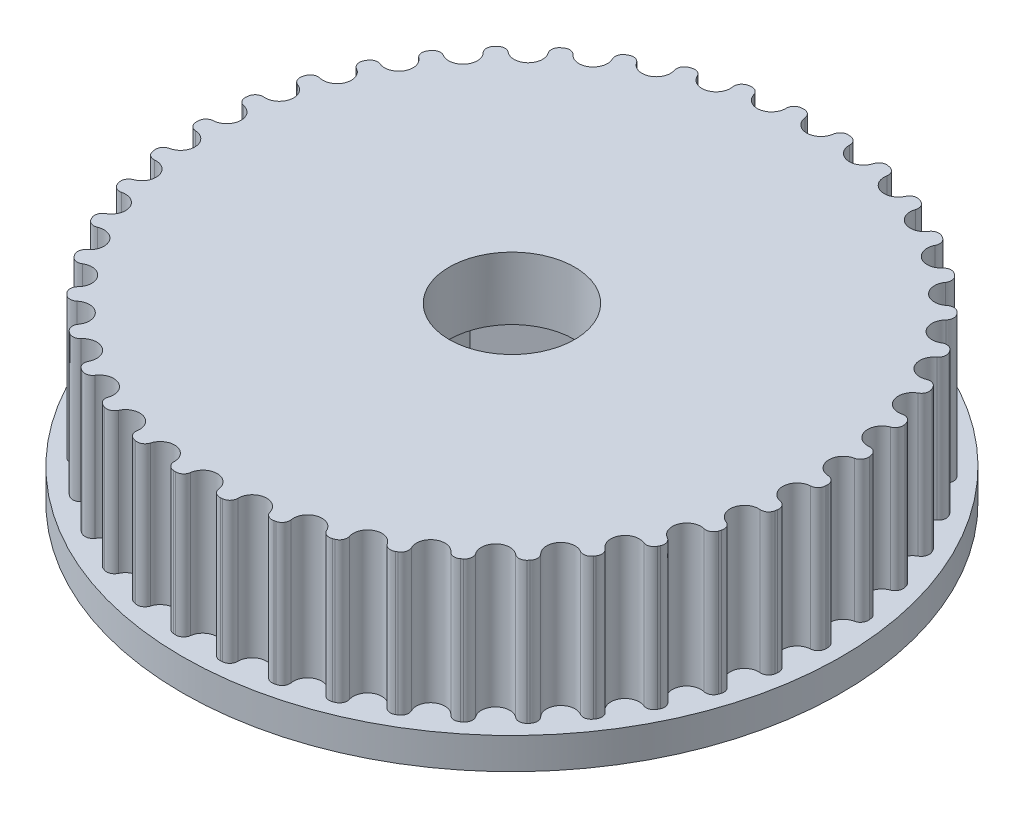
SolidWorks part; units mm, degrees
ref_plane "Front Plane" through (0, 0, 0) normal (0, 0, 1) x (1, 0, 0)
ref_plane "Top Plane" through (0, 0, 0) normal (0, 1, 0) x (1, 0, 0)
ref_plane "Right Plane" through (0, 0, 0) normal (1, 0, 0) x (0, 0, -1)
sketch "Эскиз1" plane through (0, 0, 0) normal (0, 1, 0) x (1, 0, 0)
  circle A0 centre (0, 0) radius 21
  dimension "D1" = 42
extrude "Бобышка-Вытянуть1" add sketch "Эскиз1" along normal blind 2
sketch "Эскиз2" plane through (0, 2, 0) normal (0, 1, 0) x (1, 0, 0)
  circle A0 centre (0, 0) radius 20.065
  dimension "D1" = 40.13
extrude "Бобышка-Вытянуть2" add sketch "Эскиз2" along normal blind 9
sketch "Эскиз3" plane through (0, 11, 0) normal (0, 1, 0) x (1, 0, 0)
  line L0 (0, 0) -> (-1.0785, 23.3144)
  line L1 (0, 0) -> (1.0782, 23.3144)
  line L2 (1.0782, 23.3144) -> (-1.0785, 23.3144)
  circle A0 centre (0, 0) radius 20.065
  circle A1 centre (0, 0) radius 18.785
  circle A2 centre (-0.0001, 19.695) radius 0.91
  circle M2 centre (0, 0) radius 20.065
  dimension "D1" = 40.13
  dimension "D2" = 37.57
  dimension "D3" = 1.82
extrude "Вырез-Вытянуть1" cut sketch "Эскиз3" against normal blind 9 contours A2 A0 | A2 L1 M2 | A2 L0 M2
fillet "Скругление1" radius 0.5 2 edges at (-0.9272, 6.5, -20.0436) (0.927, 6.5, -20.0436)
pattern_circular "Круговой массив1" count 42 over 360 about axis through (0, 0, 0) along (0, 1, 0) of "Скругление1", "Вырез-Вытянуть1"
sketch "Эскиз4" plane through (0, 11, 0) normal (0, 1, 0) x (1, 0, 0)
  circle A0 centre (0, 0) radius 4
  dimension "D1" = 8
extrude "Вырез-Вытянуть2" cut sketch "Эскиз4" against normal through all
sketch "Эскиз5" plane through (0, 0, 0) normal (0, -1, 0) x (1, 0, 0)
  line L1 (0, 7.3) -> (-6.322, 3.65)
  line L2 (-6.322, 3.65) -> (-6.322, -3.65)
  line L3 (-6.322, -3.65) -> (0, -7.3)
  line L4 (0, -7.3) -> (6.322, -3.65)
  line L5 (6.322, -3.65) -> (6.322, 3.65)
  line L6 (6.322, 3.65) -> (0, 7.3)
  circle A0 centre (0, 0) radius 6.322 construction
  dimension "D1" = 14.6
extrude "Вырез-Вытянуть3" cut sketch "Эскиз5" against normal blind 7
